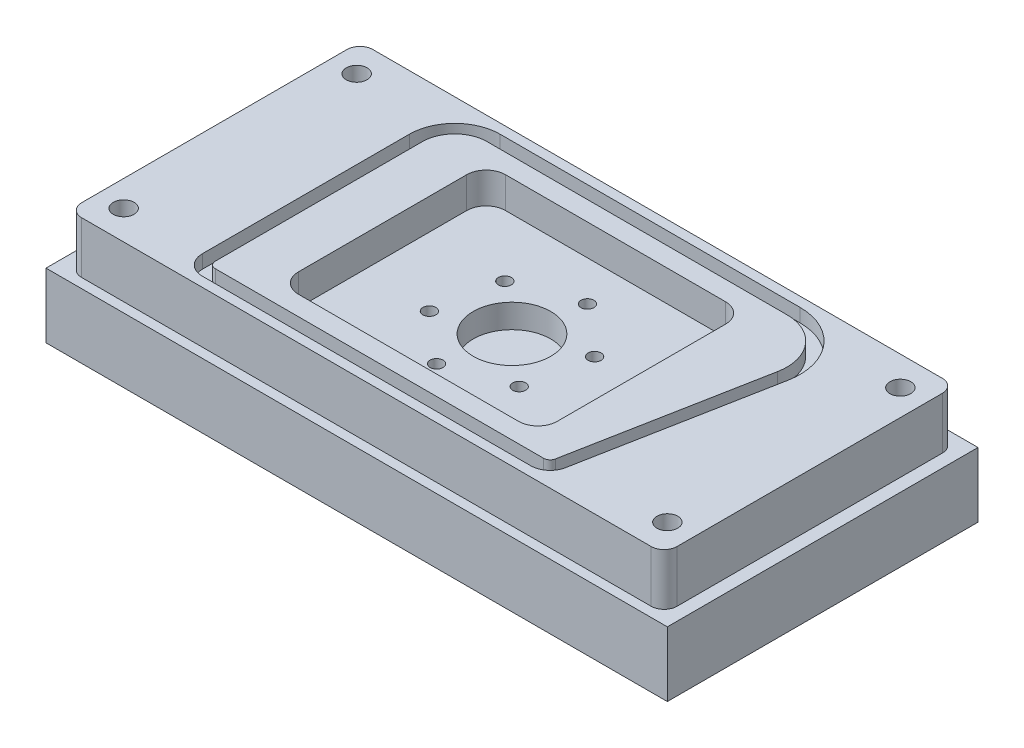
SolidWorks part; units mm, degrees
ref_plane "Front Plane" through (0, 0, 0) normal (0, 0, 1) x (1, 0, 0)
ref_plane "Top Plane" through (0, 0, 0) normal (0, 1, 0) x (1, 0, 0)
ref_plane "Right Plane" through (0, 0, 0) normal (1, 0, 0) x (0, 0, -1)
sketch "Sketch1" plane through (0, 0, 0) normal (0, 1, 0) x (1, 0, 0)
  line L0 (-76.2, 38.1) -> (76.2, 38.1)
  line L1 (-76.2, -38.1) -> (76.2, -38.1)
  line L2 (-76.2, 38.1) -> (-76.2, -38.1)
  line L3 (76.2, 38.1) -> (76.2, -38.1)
  dimension "D1" = 38.1
  dimension "D2" = 38.1
  dimension "D3" = 76.2
  dimension "D4" = 76.2
  dimension "D5" = 152.4
  dimension "D6" = 152.4
extrude "Boss-Extrude1" add sketch "Sketch1" along normal blind 28.575
sketch "Sketch2" plane through (0, 28.575, 0) normal (0, 1, 0) x (1, 0, 0)
  circle A0 centre (0, 0) radius 9.525
  dimension "D1" = 19.05
extrude "Cut-Extrude1" cut sketch "Sketch2" against normal blind 13.462
sketch "Sketch4" plane through (0, 28.575, 0) normal (0, 1, 0) x (1, 0, 0)
  line L4 (-47.3837, 22.225) -> (-47.3837, -28.575)
  line L5 (-42.6212, -33.3375) -> (37.9352, -33.3375)
  line L6 (51.325, 16.3831) -> (42.614, -29.464)
  line L7 (-36.2712, 33.3375) -> (37.2886, 33.3375)
  line L12 (-47.3837, 22.225) -> (-47.3837, -28.575)
  line L13 (-42.6212, -33.3375) -> (37.9352, -33.3375)
  line L14 (51.325, 16.3831) -> (42.614, -29.464)
  line L15 (-36.2712, 33.3375) -> (37.2886, 33.3375)
  line L16 (-44.2087, 22.225) -> (-44.2087, -28.575)
  line L17 (-42.6212, -30.1625) -> (37.9352, -30.1625)
  line L18 (48.2058, 16.9757) -> (39.4948, -28.8713)
  line L19 (-36.2712, 30.1625) -> (37.2886, 30.1625)
  arc A4 (-47.3837, -28.575) -> (-42.6212, -33.3375) centre (-42.6212, -28.575) ccw
  arc A5 (42.614, -29.464) -> (37.9352, -33.3375) centre (37.9352, -28.575) cw
  arc A6 (51.325, 16.3831) -> (37.2886, 33.3375) centre (37.2886, 19.05) ccw
  arc A7 (-36.2712, 33.3375) -> (-47.3837, 22.225) centre (-36.2712, 22.225) ccw
  arc A8 (-47.3837, -28.575) -> (-42.6212, -33.3375) centre (-42.6212, -28.575) ccw
  arc A9 (42.614, -29.464) -> (37.9352, -33.3375) centre (37.9352, -28.575) cw
  arc A10 (51.325, 16.3831) -> (37.2886, 33.3375) centre (37.2886, 19.05) ccw
  arc A11 (-36.2712, 33.3375) -> (-47.3837, 22.225) centre (-36.2712, 22.225) ccw
  arc A12 (-44.2087, -28.575) -> (-42.6212, -30.1625) centre (-42.6212, -28.575) ccw
  arc A13 (39.4948, -28.8713) -> (37.9352, -30.1625) centre (37.9352, -28.575) cw
  arc A14 (48.2058, 16.9757) -> (37.2886, 30.1625) centre (37.2886, 19.05) ccw
  arc A15 (-36.2712, 30.1625) -> (-44.2087, 22.225) centre (-36.2712, 22.225) ccw
  point P0 (-45.7962, -31.75)
  point P1 (-45.7962, 31.75)
  point P2 (52.6288, 31.75)
  point P3 (40.5638, -31.75)
  dimension "D1" = 45.7962
  dimension "D2" = 45.7962
  dimension "D3" = 52.6288
  dimension "D4" = 40.5638
  dimension "D5" = 31.75
  dimension "D6" = 31.75
  dimension "D7" = 31.75
  dimension "D8" = 31.75
extrude "Cut-Extrude3" cut sketch "Sketch4" along direction (0, 1, 0) on the side against the normal blind 3.302 contours L7 A7 L4 A4 L5 A5 L6 A6 A15 L19 A14 L18 A13 L17 A12 L16
sketch "Sketch7" plane through (0, 28.575, 0) normal (0, 1, 0) x (1, 0, 0)
  line L0 (31.75, 20.6375) -> (31.75, -20.6375)
  line L4 (-31.75, 20.6375) -> (-31.75, -20.6375)
  line L16 (26.9875, 25.4) -> (-26.9875, 25.4)
  line L17 (-31.75, 20.6375) -> (-31.75, -20.6375)
  line L18 (-26.9875, -25.4) -> (26.9875, -25.4)
  arc A0 (31.75, -20.6375) -> (26.9875, -25.4) centre (26.9875, -20.6375) cw
  arc A1 (-31.75, -20.6375) -> (-26.9875, -25.4) centre (-26.9875, -20.6375) ccw
  arc A2 (31.75, 20.6375) -> (26.9875, 25.4) centre (26.9875, 20.6375) ccw
  arc A3 (-26.9875, 25.4) -> (-31.75, 20.6375) centre (-26.9875, 20.6375) ccw
  dimension "D3" = 31.75
  dimension "D1" = 25.4
  dimension "D4" = 4.7625
  dimension "D2" = 25.4
  dimension "D5" = 31.75
extrude "Cut-Extrude4" cut sketch "Sketch7" against normal blind 7.62
hole_wizard "#7 (0.201) Diameter Hole1" positions "Sketch9" profile "Sketch8" hole size "#7" standard "Ansi Inch"
sketch "Sketch9" plane through (0, 28.575, 0) normal (0, 1, 0) x (-1, 0, 0)
  line L0 (-76.2, -38.1) -> (76.2, -38.1) construction
  line L1 (76.2, -38.1) -> (76.2, 38.1) construction
  line L2 (76.2, 38.1) -> (-76.2, 38.1) construction
  line L3 (-76.2, 38.1) -> (-76.2, -38.1) construction
  point P0 (66.675, -28.575)
  point P1 (-66.675, -28.575)
  point P3 (-66.675, 28.575)
  point P5 (66.675, 28.575)
  dimension "D1" = 9.525
  dimension "D2" = 9.525
  dimension "D3" = 9.525
  dimension "D4" = 9.525
  dimension "D5" = 9.525
  dimension "D6" = 9.525
  dimension "D7" = 9.525
  dimension "D8" = 9.525
sketch "Sketch8" plane through (-66.675, 28.575, -28.575) normal (1, 0, 0) x (0, 0, 1)
  line L0 (0, 0) -> (0, 15.8086)
  line L1 (0, 15.8086) -> (2.5527, 14.2748)
  line L2 (2.5527, 14.2748) -> (2.5527, 0)
  line L5 (2.5527, 0) -> (0, 0)
  line L10 (0, 15.8086) -> (-2.5527, 14.2748) construction
  line L11 (0, -6.35) -> (0, 107.95) construction
  dimension "Hole Dia." = 5.1054
  dimension "Hole Depth" = 14.2748
  dimension "Drill Angle" = 118
sketch "Sketch10" plane through (0, 28.575, 0) normal (0, 1, 0) x (1, 0, 0)
  line L0 (-73.025, 32.545) -> (-73.025, -32.545)
  line L1 (73.025, 32.545) -> (73.025, -32.545)
  line L2 (-69.85, 35.72) -> (69.85, 35.72)
  line L3 (69.85, -35.72) -> (-69.85, -35.72)
  line L4 (-76.2, 38.1) -> (-76.2, -38.1) construction
  line L5 (76.2, -38.1) -> (76.2, 38.1) construction
  line L6 (76.2, 38.1) -> (-76.2, 38.1) construction
  line L7 (-76.2, -38.1) -> (76.2, -38.1) construction
  arc A0 (-73.025, -32.545) -> (-69.85, -35.72) centre (-69.85, -32.545) ccw
  arc A1 (69.85, -35.72) -> (73.025, -32.545) centre (69.85, -32.545) ccw
  arc A2 (73.025, 32.545) -> (69.85, 35.72) centre (69.85, 32.545) ccw
  arc A3 (-69.85, 35.72) -> (-73.025, 32.545) centre (-69.85, 32.545) ccw
  dimension "D5" = 3.175
  dimension "D1" = 3.175
  dimension "D2" = 3.175
  dimension "D3" = 2.38
  dimension "D4" = 2.38
extrude "Cut-Extrude5" cut sketch "Sketch10" against normal blind 12.7 flip side to cut
hole_wizard "1/8 (0.125) Diameter Hole1" positions "Sketch14" profile "Sketch13" hole size "1/8" standard "Ansi Inch"
sketch "Sketch14" plane through (0, 20.955, 0) normal (0, 1, 0) x (-1, 0, 0)
  line L0 (-14.9644, -5.2992) -> (0, 0)
  line L2 (0, 0) -> (-13.4642, 0)
  point P0 (-14.9644, -5.2992)
  dimension "D1" = 19.5
  dimension "D2" = 15.875
sketch "Sketch13" plane through (14.9644, 20.955, -5.2992) normal (1, 0, 0) x (0, 0, 1)
  line L0 (0, 0) -> (0, 18.4291)
  line L1 (0, 18.4291) -> (1.5875, 17.4752)
  line L2 (1.5875, 17.4752) -> (1.5875, 0)
  line L5 (1.5875, 0) -> (0, 0)
  line L10 (0, 18.4291) -> (-1.5875, 17.4752) construction
  line L11 (0, -6.35) -> (0, 107.95) construction
  dimension "Hole Dia." = 3.175
  dimension "Hole Depth" = 17.4752
  dimension "Drill Angle" = 118
pattern_circular "CirPattern1" count 6 over 360 about axis through (0, 0, 0) along (0, 1, 0) of "1/8 (0.125) Diameter Hole1"
